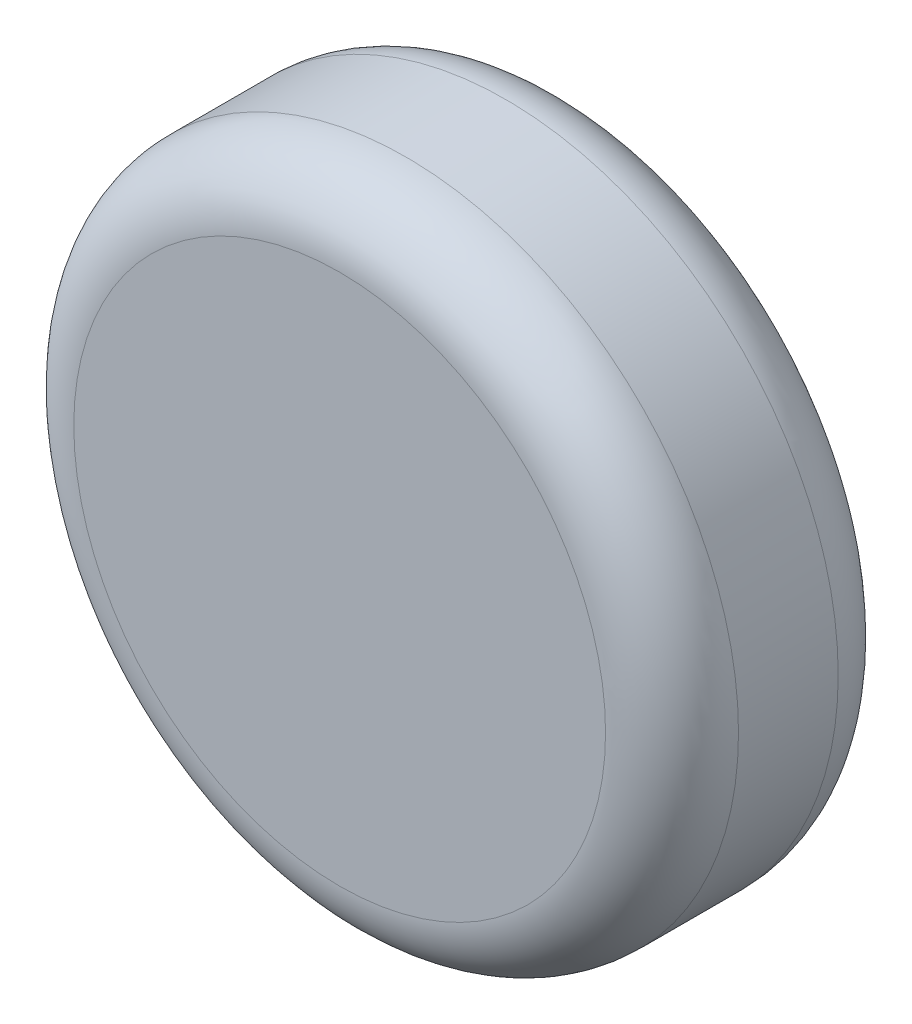
SolidWorks part; units mm, degrees
ref_plane "Front Plane" through (0, 0, 0) normal (0, 0, 1) x (1, 0, 0)
ref_plane "Top Plane" through (0, 0, 0) normal (0, 1, 0) x (1, 0, 0)
ref_plane "Right Plane" through (0, 0, 0) normal (1, 0, 0) x (0, 0, -1)
sketch "Sketch1" plane through (0, 0, 0) normal (0, 0, 1) x (1, 0, 0)
  circle A0 centre (0, 0) radius 12.7
  dimension "D1" = 25.4
extrude "Boss-Extrude1" add sketch "Sketch1" along normal blind 8.89
sketch "Sketch2" plane through (0, 0, 0) normal (0, 0, -1) x (-1, 0, 0)
  circle A0 centre (0, 0) radius 2.54
  dimension "D1" = 5.08
extrude "Cut-Extrude1" cut sketch "Sketch2" against normal blind 6.35
fillet "Fillet1" radius 2.54 2 edges at (12.7, 0, 0) (12.7, 0, 8.89)
